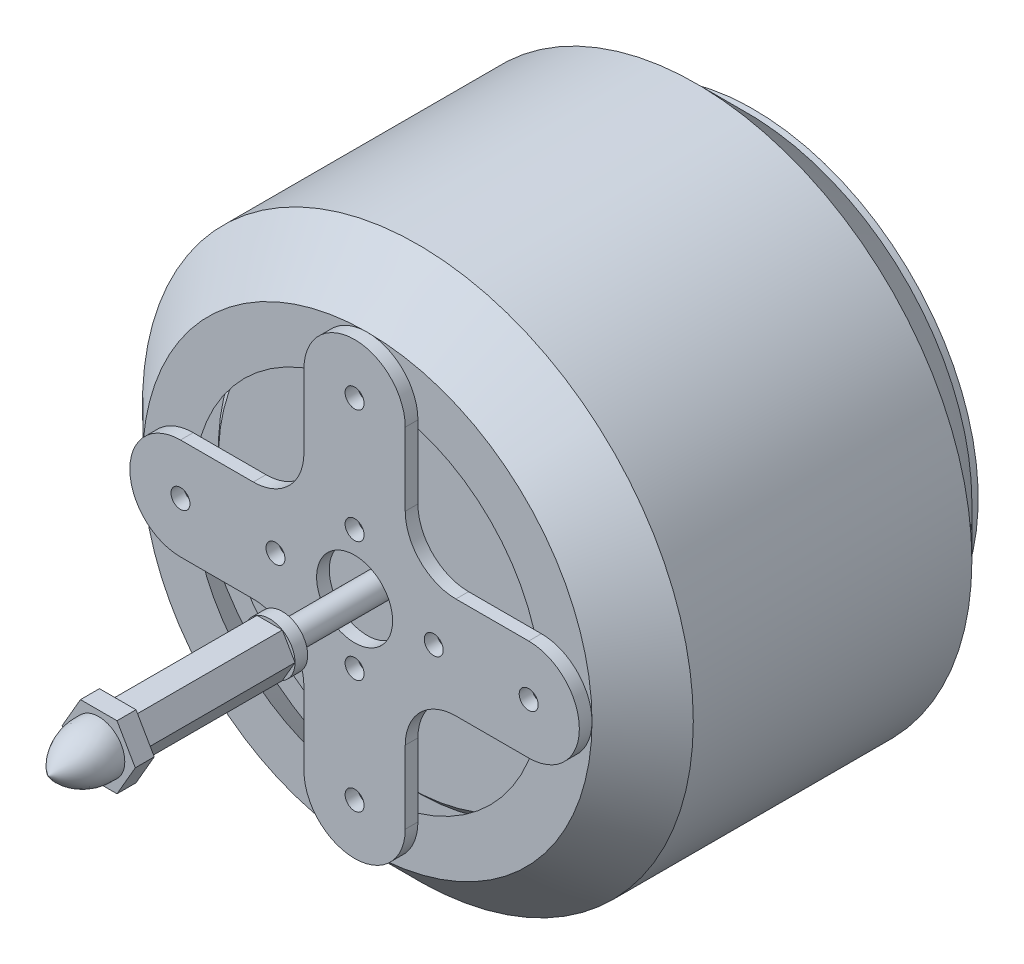
SolidWorks part; units mm, degrees
ref_plane "Ön Düzlem" through (0, 0, 0) normal (0, 0, 1) x (1, 0, 0)
ref_plane "Üst Düzlem" through (0, 0, 0) normal (0, 1, 0) x (1, 0, 0)
ref_plane "Sağ Düzlem" through (0, 0, 0) normal (1, 0, 0) x (0, 0, -1)
sketch "Çizim1" plane through (0, 0, 0) normal (0, 0, 1) x (1, 0, 0)
  line L0 (8, 27.5) -> (8, 8)
  line L1 (8, 8) -> (27.5, 8)
  line L2 (27.5, -8) -> (8, -8)
  line L3 (8, -8) -> (8, -27.5)
  line L4 (-8, -27.5) -> (-8, -8)
  line L5 (-8, -8) -> (-27.5, -8)
  line L6 (-27.5, 8) -> (-8, 8)
  line L7 (-8, 8) -> (-8, 27.5)
  circle A0 centre (0, 0) radius 6
  arc A1 (8, 27.5) -> (-8, 27.5) centre (0, 27.5) ccw
  circle A2 centre (0, 9.5) radius 1.5
  circle A3 centre (0, -9.5) radius 1.5
  circle A4 centre (-12.5, 0) radius 1.5
  circle A5 centre (12.5, 0) radius 1.5
  circle A6 centre (0, 27.5) radius 1.5
  circle A7 centre (27.5, 0) radius 1.5
  circle A8 centre (0, -27.5) radius 1.5
  circle A9 centre (-27.5, 0) radius 1.5
  arc A10 (27.5, -8) -> (27.5, 8) centre (27.5, 0) ccw
  arc A11 (-8, -27.5) -> (8, -27.5) centre (0, -27.5) ccw
  arc A12 (-27.5, 8) -> (-27.5, -8) centre (-27.5, 0) ccw
  point P11 (0, 0)
  point P16 (0, 0)
  point P25 (0, 0)
  point P32 (0, 0)
  point P45 (0, 0)
  dimension "D1" = 2
  dimension "D2" = 2
  dimension "D3" = 4
  dimension "D4" = 4
  dimension "D5" = 4
extrude "Yükseklik-Ekstrüzyon1" add sketch "Çizim1" along normal blind 2
fillet "Radyus1" radius 8 4 edges at (8, -8, 1) (-8, -8, 1) (-8, 8, 1) (8, 8, 1)
sketch "Çizim4" plane through (0, 0, 0) normal (1, 0, 0) x (0, 0, -1)
  line L0 (0, 27.5) -> (0, 35.5)
  line L1 (8, 35.5) -> (8, 31.5)
  line L2 (53.4142, 30.0858) -> (53.4142, 0)
  line L3 (8, 43.5) -> (0, 35.5)
  line L4 (8, 35.5) -> (0, 27.5)
  line L5 (8, 31.5) -> (6.5858, 30.0858)
  line L6 (6.5858, 30.0858) -> (6.5858, 0)
  line L7 (6.5858, 0) -> (53.4142, 0)
  line L9 (52, 43.5) -> (8, 43.5)
  line L10 (52, 31.5) -> (53.4142, 30.0858)
  line L11 (52, 35.5) -> (60, 27.5)
  line L12 (52, 43.5) -> (60, 35.5)
  line L13 (52, 35.5) -> (52, 31.5)
  line L14 (60, 27.5) -> (60, 35.5)
revolve "Döndür1" add sketch "Çizim4" angle 360 about L7
sketch "Çizim5" plane through (0, 0, -60) normal (0, 0, -1) x (-1, 0, 0)
  circle A0 centre (0, 0) radius 35.5
extrude "Yükseklik-Ekstrüzyon2" add sketch "Çizim5" along normal blind 1
sketch "Çizim6" plane through (0, 0, -6.5858) normal (0, 0, 1) x (1, 0, 0)
  circle A0 centre (0, 0) radius 2
extrude "Yükseklik-Ekstrüzyon3" add sketch "Çizim6" along normal blind 20
sketch "Çizim7" plane through (0, 0, 13.4142) normal (0, 0, 1) x (1, 0, 0)
  circle A0 centre (0, 0) radius 4
extrude "Yükseklik-Ekstrüzyon4" add sketch "Çizim7" along normal blind 2
sketch "Çizim9" plane through (0, 0, 15.4142) normal (0, 0, 1) x (1, 0, 0)
  line L1 (4, 0) -> (2, 3.4641)
  line L2 (2, 3.4641) -> (-2, 3.4641)
  line L3 (-2, 3.4641) -> (-4, 0)
  line L4 (-4, 0) -> (-2, -3.4641)
  line L5 (-2, -3.4641) -> (2, -3.4641)
  line L6 (2, -3.4641) -> (4, 0)
  circle A0 centre (0, 0) radius 3.4641 construction
extrude "Yükseklik-Ekstrüzyon5" add sketch "Çizim9" along normal blind 24
sketch "Çizim10" plane through (0, 0, 39.4142) normal (0, 0, 1) x (1, 0, 0)
  line L1 (5.7735, 0) -> (2.8868, 5)
  line L2 (2.8868, 5) -> (-2.8868, 5)
  line L3 (-2.8868, 5) -> (-5.7735, 0)
  line L4 (-5.7735, 0) -> (-2.8868, -5)
  line L5 (-2.8868, -5) -> (2.8868, -5)
  line L6 (2.8868, -5) -> (5.7735, 0)
  circle A0 centre (0, 0) radius 5 construction
extrude "Yükseklik-Ekstrüzyon6" add sketch "Çizim10" along normal blind 3
sketch "Çizim11" plane through (0, 0, 0) normal (1, 0, 0) x (0, 0, -1)
  line L0 (-42.4142, 0) -> (-50.4142, 0)
  line L1 (-42.4142, 5) -> (-42.4142, 0) construction
  line L2 (-42.4142, 4.1165) -> (-42.4142, 0)
  arc A0 (-42.4142, 4.1165) -> (-50.4142, 0) centre (-42.9986, -4.5795) ccw
revolve "Döndür2" add sketch "Çizim11" angle 360 about L0
